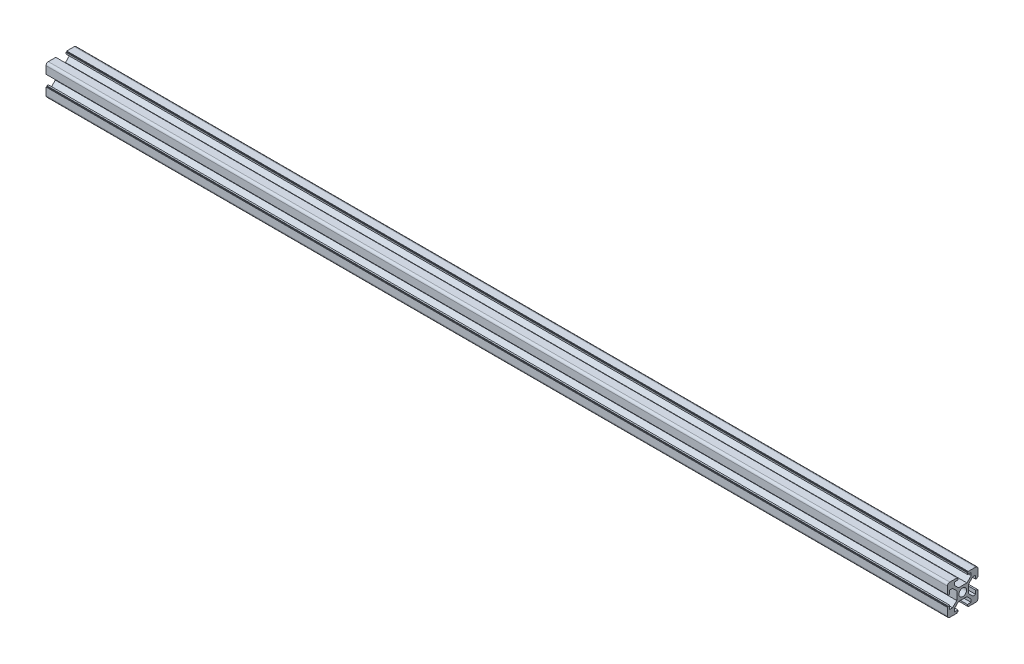
SolidWorks part; units mm, degrees
ref_plane "前视基准面" through (0, 0, 0) normal (0, 0, 1) x (1, 0, 0)
ref_plane "上视基准面" through (0, 0, 0) normal (0, 1, 0) x (1, 0, 0)
ref_plane "右视基准面" through (0, 0, 0) normal (1, 0, 0) x (0, 0, -1)
sketch "草图1" plane through (0, 0, 0) normal (0, 1, 0) x (1, 0, 0)
  line L0 (0, 0) -> (590, 0)
  dimension "D1" = 590
other "铝型材 20 X 20 X R1.5(1)"
ref_plane "基准面1" through (0, 0, 0) normal (1, 0, 0) x (0, 0, -1)
sketch "Sketch1" plane through (0, 0, 0) normal (1, 0, 0) x (0, 0, -1)
  line L0 (-3.6, 10) -> (-3.6, 9.5)
  line L1 (-3.6, 9.5) -> (-3.1, 9.5)
  line L2 (-3.1, 9.5) -> (-3.1, 8.5)
  line L3 (-3.1, 8.5) -> (-5.5, 8.5)
  line L4 (-8.5, -10) -> (-3.6, -10)
  line L5 (-10, -8.5) -> (-10, -3.6)
  line L6 (8.5, 10) -> (3.6, 10)
  line L7 (10, 8.5) -> (10, 3.6)
  line L8 (0, 14.8756) -> (0, 0) construction
  line L9 (0, 0) -> (14.1675, 0) construction
  line L10 (-5.5, 8.5) -> (-5.5, 6.65)
  line L11 (-5.5, 6.65) -> (-2.75, 3.9)
  line L12 (-2.75, 3.9) -> (2.75, 3.9)
  line L13 (5.5, 6.65) -> (2.75, 3.9)
  line L14 (5.5, 8.5) -> (5.5, 6.65)
  line L15 (3.1, 8.5) -> (5.5, 8.5)
  line L16 (3.1, 9.5) -> (3.1, 8.5)
  line L17 (3.6, 9.5) -> (3.1, 9.5)
  line L18 (3.6, 10) -> (3.6, 9.5)
  line L19 (-3.6, 10) -> (-8.5, 10)
  line L20 (10, 3.6) -> (9.5, 3.6)
  line L21 (9.5, 3.6) -> (9.5, 3.1)
  line L22 (9.5, 3.1) -> (8.5, 3.1)
  line L23 (8.5, 3.1) -> (8.5, 5.5)
  line L24 (8.5, 5.5) -> (6.65, 5.5)
  line L25 (6.65, 5.5) -> (3.9, 2.75)
  line L26 (3.9, 2.75) -> (3.9, -2.75)
  line L27 (6.65, -5.5) -> (3.9, -2.75)
  line L28 (8.5, -5.5) -> (6.65, -5.5)
  line L29 (8.5, -3.1) -> (8.5, -5.5)
  line L30 (9.5, -3.1) -> (8.5, -3.1)
  line L31 (9.5, -3.6) -> (9.5, -3.1)
  line L32 (10, -3.6) -> (9.5, -3.6)
  line L33 (3.6, -10) -> (3.6, -9.5)
  line L34 (3.6, -9.5) -> (3.1, -9.5)
  line L35 (3.1, -9.5) -> (3.1, -8.5)
  line L36 (3.1, -8.5) -> (5.5, -8.5)
  line L37 (5.5, -8.5) -> (5.5, -6.65)
  line L38 (5.5, -6.65) -> (2.75, -3.9)
  line L39 (2.75, -3.9) -> (-2.75, -3.9)
  line L40 (-5.5, -6.65) -> (-2.75, -3.9)
  line L41 (-5.5, -8.5) -> (-5.5, -6.65)
  line L42 (-3.1, -8.5) -> (-5.5, -8.5)
  line L43 (-3.1, -9.5) -> (-3.1, -8.5)
  line L44 (-3.6, -9.5) -> (-3.1, -9.5)
  line L45 (-3.6, -10) -> (-3.6, -9.5)
  line L46 (-10, -3.6) -> (-9.5, -3.6)
  line L47 (-9.5, -3.6) -> (-9.5, -3.1)
  line L48 (-9.5, -3.1) -> (-8.5, -3.1)
  line L49 (-8.5, -3.1) -> (-8.5, -5.5)
  line L50 (-8.5, -5.5) -> (-6.65, -5.5)
  line L51 (-6.65, -5.5) -> (-3.9, -2.75)
  line L52 (-3.9, -2.75) -> (-3.9, 2.75)
  line L53 (-6.65, 5.5) -> (-3.9, 2.75)
  line L54 (-8.5, 5.5) -> (-6.65, 5.5)
  line L55 (-8.5, 3.1) -> (-8.5, 5.5)
  line L56 (-9.5, 3.1) -> (-8.5, 3.1)
  line L57 (-9.5, 3.6) -> (-9.5, 3.1)
  line L58 (-10, 3.6) -> (-9.5, 3.6)
  line L59 (3.6, -10) -> (8.5, -10)
  line L60 (-10, 3.6) -> (-10, 8.5)
  line L61 (10, -3.6) -> (10, -8.5)
  circle A0 centre (0, 0) radius 2.5
  arc A1 (-10, 8.5) -> (-8.5, 10) centre (-8.5, 8.5) cw
  arc A2 (10, 8.5) -> (8.5, 10) centre (8.5, 8.5) ccw
  arc A3 (-8.5, -10) -> (-10, -8.5) centre (-8.5, -8.5) cw
  arc A4 (8.5, -10) -> (10, -8.5) centre (8.5, -8.5) ccw
  point P0 (-10, 0)
  point P1 (10, 0)
  point P2 (0, 10)
  point P3 (0, -10)
  point P4 (0, 0)
  point P5 (-10, -10)
  point P6 (10, -10)
  point P7 (10, 10)
  point P8 (-10, 10)
  point P13 (0, 0)
  point P36 (-10, 10)
  point P39 (10, 10)
  dimension "D1" = 11
  dimension "D2" = 20
  dimension "D3" = 6.2
  dimension "D4" = 7.2
  dimension "D5" = 6.1
  dimension "D6" = 5
  dimension "D7" = 1.5
  dimension "D8" = 45
  dimension "D9" = 0.5
  dimension "D10" = 1
  dimension "D11" = 5.5
